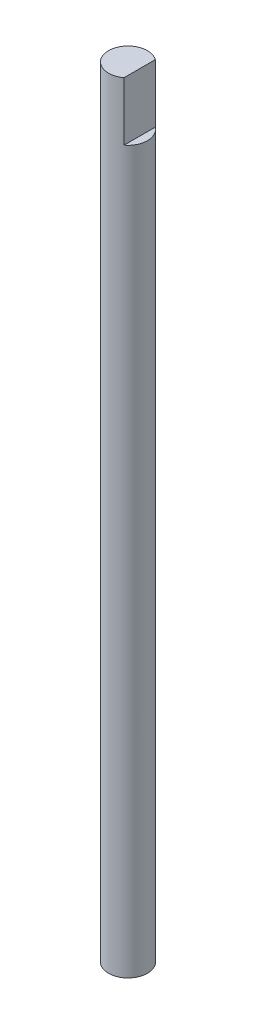
SolidWorks part; units mm, degrees
material "Chrome Stainless Steel"
ref_plane "Front Plane" through (0, 0, 0) normal (0, 0, 1) x (1, 0, 0)
ref_plane "Top Plane" through (0, 0, 0) normal (0, 1, 0) x (1, 0, 0)
ref_plane "Right Plane" through (0, 0, 0) normal (1, 0, 0) x (0, 0, -1)
sketch "Sketch1" plane through (0, 0, 0) normal (0, 1, 0) x (1, 0, 0)
  circle A0 centre (0, 0) radius 5
  dimension "D1" = 10
extrude "Base" add sketch "Sketch1" along normal blind 200
sketch "Sketch2" plane through (0, 0, 0) normal (0, 0, 1) x (1, 0, 0)
  line L0 (5, 0) -> (5, 200) construction
  line L1 (3, 201.135) -> (5, 201.135)
  line L2 (3, 201.135) -> (3, 185)
  line L3 (3, 185) -> (5, 185)
  line L4 (5, 201.135) -> (5, 185)
  line L5 (5, 200) -> (-5, 200) construction
  dimension "D1" = 15
  dimension "D2" = 2
extrude "Slot" cut sketch "Sketch2" against normal through all both and the other way through all
